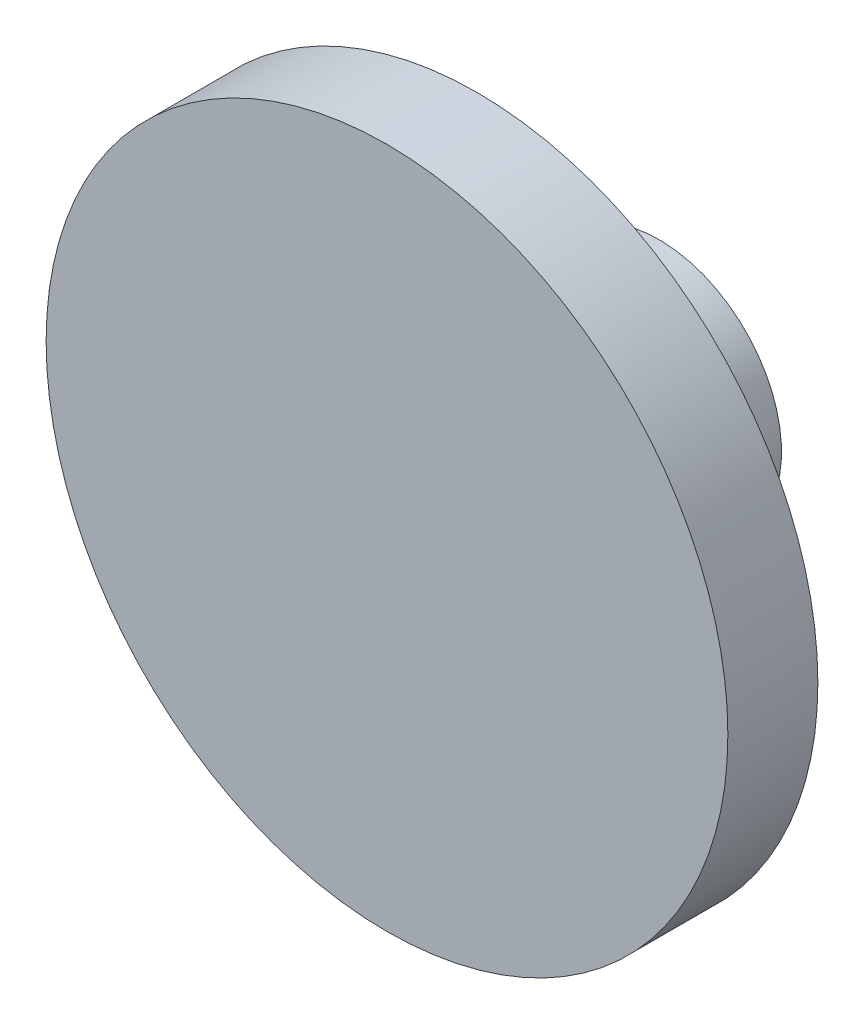
SolidWorks part; units mm, degrees
material "ABS"
ref_plane "Front Plane" through (0, 0, 0) normal (0, 0, 1) x (1, 0, 0)
ref_plane "Top Plane" through (0, 0, 0) normal (0, 1, 0) x (1, 0, 0)
ref_plane "Right Plane" through (0, 0, 0) normal (1, 0, 0) x (0, 0, -1)
sketch "Sketch2" plane through (0, 0, 0) normal (1, 0, 0) x (0, 0, -1)
  line L2 (-35.5, -5.2518) -> (-35.5, 39.2482)
  line L3 (-35.5, 39.2482) -> (-23.75, 39.2482)
  line L4 (-23.75, 39.2482) -> (-23.75, 10.7482)
  line L7 (-23.75, 10.7482) -> (0, 10.7482)
  line L8 (0, 10.7482) -> (0, -5.2518)
  line L9 (0, -5.2518) -> (-35.5, -5.2518)
revolve "Revolve1" add sketch "Sketch2" angle 360 about L9
